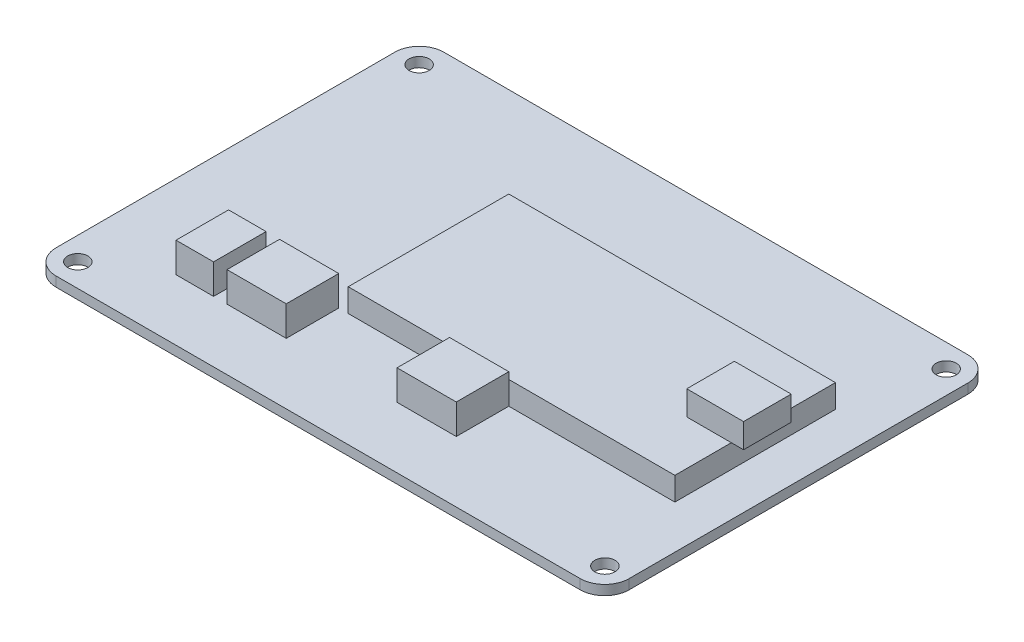
SolidWorks part; units mm, degrees
ref_plane "Front Plane" through (0, 0, 0) normal (0, 0, 1) x (1, 0, 0)
ref_plane "Top Plane" through (0, 0, 0) normal (0, 1, 0) x (1, 0, 0)
ref_plane "Right Plane" through (0, 0, 0) normal (1, 0, 0) x (0, 0, -1)
sketch "Sketch1" plane through (0, 0, 0) normal (0, 1, 0) x (1, 0, 0)
  line L0 (0, 31.75) -> (0, -31.75) construction
  line L1 (-46.925, 31.75) -> (46.925, 31.75)
  line L2 (-46.925, 31.75) -> (-46.925, -31.75)
  line L3 (-46.925, -31.75) -> (46.925, -31.75)
  line L4 (46.925, 31.75) -> (46.925, -31.75)
  line L5 (-46.925, 31.75) -> (46.925, -31.75) construction
  line L6 (-46.925, -31.75) -> (46.925, 31.75) construction
  line L7 (-46.925, 0) -> (46.925, 0) construction
  circle A0 centre (-43.1625, 27.95) radius 1.65
  circle A1 centre (43.1625, 27.95) radius 1.65
  circle A2 centre (43.1625, -27.95) radius 1.65
  circle A3 centre (-43.1625, -27.95) radius 1.65
  point P0 (0, 0)
  dimension "D3" = 3.3
  dimension "D4" = 86.325
  dimension "D1" = 63.5
  dimension "D2" = 93.85
  dimension "D5" = 55.9
extrude "Boss-Extrude1" add sketch "Sketch1" along normal blind 1.6
fillet "Fillet1" radius 4 4 edges at (-46.925, 0.8, -31.75) (46.925, 0.8, -31.75) (46.925, 0.8, 31.75) (-46.925, 0.8, 31.75)
sketch "Sketch2" plane through (0, 1.6, 0) normal (0, 1, 0) x (1, 0, 0)
  line L0 (-46.925, 0) -> (46.925, 0) construction
  line L1 (-46.925, 27.75) -> (-46.925, -27.75) construction
  line L2 (46.925, -27.75) -> (46.925, 27.75) construction
  line L4 (-13.675, 13.15) -> (39.825, 13.15)
  line L5 (-13.675, 13.15) -> (-13.675, -13.15)
  line L6 (-13.675, -13.15) -> (39.825, -13.15)
  line L7 (39.825, 13.15) -> (39.825, -13.15)
  line L8 (-13.675, 13.15) -> (39.825, -13.15) construction
  line L9 (-13.675, -13.15) -> (39.825, 13.15) construction
  point P6 (13.075, 0)
  dimension "D1" = 53.5
  dimension "D2" = 26.3
  dimension "D3" = 7.1
extrude "Boss-Extrude2" add sketch "Sketch2" along normal blind 3.8
sketch "Sketch3" plane through (0, 5.4, 0) normal (0, 1, 0) x (1, 0, 0)
  line L0 (-13.675, 0) -> (39.825, 0) construction
  line L1 (-13.675, 13.15) -> (-13.675, -13.15) construction
  line L2 (39.825, -13.15) -> (39.825, 13.15) construction
  line L4 (32.525, -3.9) -> (41.825, -3.9)
  line L5 (32.525, -3.9) -> (32.525, 3.9)
  line L6 (32.525, 3.9) -> (41.825, 3.9)
  line L7 (41.825, -3.9) -> (41.825, 3.9)
  line L8 (32.525, -3.9) -> (41.825, 3.9) construction
  line L9 (32.525, 3.9) -> (41.825, -3.9) construction
  point P6 (37.175, 0)
  dimension "D1" = 7.8
  dimension "D2" = 9.3
  dimension "D3" = 2
extrude "Boss-Extrude3" add sketch "Sketch3" along normal blind 4
sketch "Sketch4" plane through (0, 1.6, 0) normal (0, 1, 0) x (1, 0, 0)
  line L0 (-13.675, -13.15) -> (39.825, -13.15) construction
  line L1 (2.925, -13.15) -> (12.625, -13.15)
  line L2 (2.925, -13.15) -> (2.925, -21.75)
  line L3 (2.925, -21.75) -> (12.625, -21.75)
  line L4 (12.625, -13.15) -> (12.625, -21.75)
  line L5 (-13.675, 13.15) -> (-13.675, -13.15) construction
  line L7 (-15.225, -13.15) -> (-24.925, -13.15)
  line L8 (-15.225, -13.15) -> (-15.225, -21.75)
  line L9 (-15.225, -21.75) -> (-24.925, -21.75)
  line L10 (-24.925, -13.15) -> (-24.925, -21.75)
  line L11 (-27.125, -13.15) -> (-33.277, -13.15)
  line L12 (-27.125, -13.15) -> (-27.125, -21.75)
  line L13 (-27.125, -21.75) -> (-33.277, -21.75)
  line L14 (-33.277, -13.15) -> (-33.277, -21.75)
  dimension "D1" = 16.6
  dimension "D2" = 9.7
  dimension "D3" = 8.6
  dimension "D4" = 18.15
  dimension "D5" = 6.152
  dimension "D6" = 2.2
extrude "Boss-Extrude4" add sketch "Sketch4" along normal blind 4.9
